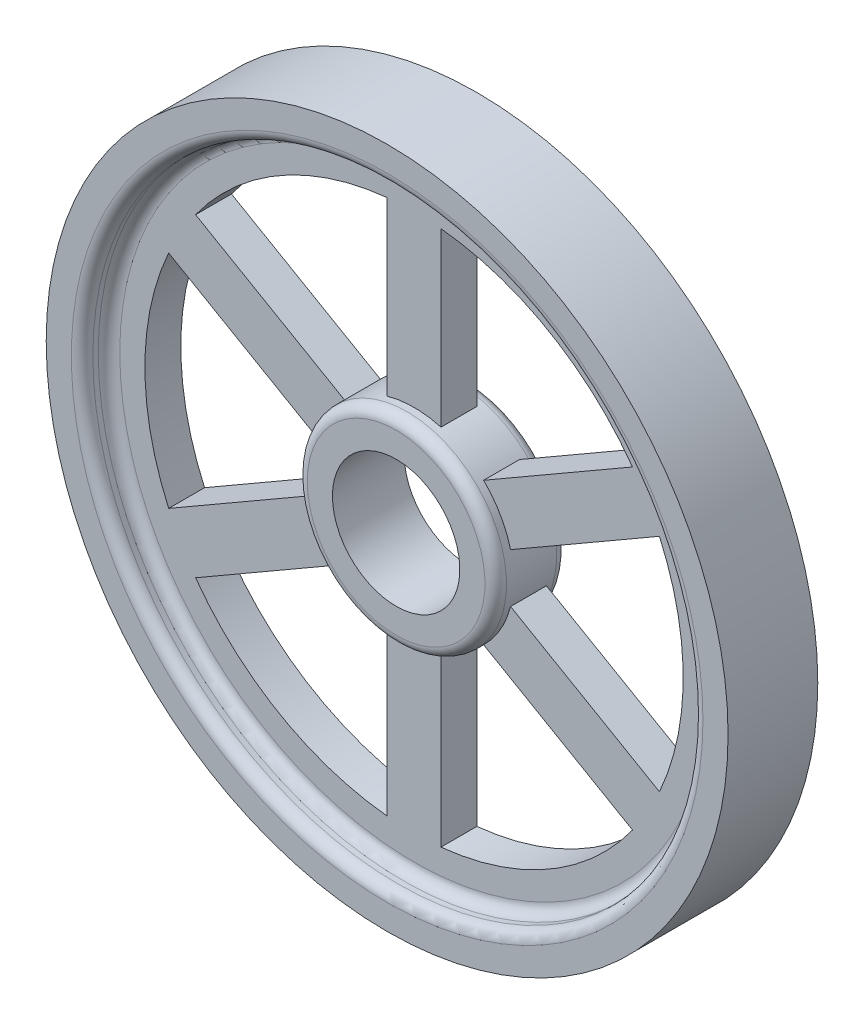
SolidWorks part; units mm, degrees
ref_plane "Front Plane" through (0, 0, 0) normal (0, 0, 1) x (1, 0, 0)
ref_plane "Top Plane" through (0, 0, 0) normal (0, 1, 0) x (1, 0, 0)
ref_plane "Right Plane" through (0, 0, 0) normal (1, 0, 0) x (0, 0, -1)
sketch "Sketch2" plane through (0, 0, 0) normal (0, 0, 1) x (1, 0, 0)
  line L0 (0, 35.4088) -> (0, -35.4088) construction
  circle A0 centre (0, 0) radius 95
  circle A2 centre (0, 0) radius 85
extrude "Boss-Extrude1" add sketch "Sketch2" along normal blind 25
ref_plane "Plane1" through (0, 0, 12.5) normal (0, 0, -1) x (-1, 0, 0)
sketch "Sketch5" plane through (0, 0, 12.5) normal (0, 0, -1) x (-1, 0, 0)
  circle A0 centre (0, 0) radius 17.75
  circle A1 centre (0, 0) radius 27.75
extrude "Boss-Extrude2" add sketch "Sketch5" along normal blind 10 and the other way blind 10 separate body
fillet "Fillet3" radius 3 2 edges at (-27.75, 0, 2.5) (-27.75, 0, 22.5)
sketch "Sketch7" plane through (0, 0, 12.5) normal (0, 0, -1) x (-1, 0, 0)
  circle A0 centre (0, 0) radius 75
  circle A1 centre (0, 0) radius 85
extrude "Boss-Extrude4" add sketch "Sketch7" along normal blind 5 and the other way blind 5
sketch "Sketch9" plane through (0, 0, 12.5) normal (0, 0, -1) x (-1, 0, 0)
  line L1 (7.5, 26.7173) -> (7.5, 74.6241)
  line L2 (-7.5, 26.7173) -> (-7.5, 74.6241)
  arc A0 (7.5, 26.7173) -> (-7.5, 26.7173) centre (0, 0) ccw
  arc A1 (7.5, 74.6241) -> (-7.5, 74.6241) centre (0, 0) ccw
extrude "Boss-Extrude5" add sketch "Sketch9" along normal blind 5 and the other way blind 5
fillet "Fillet4" radius 3 1 edges at (85, 0, 25)
fillet "Fillet8" radius 3 1 edges at (85, 0, 0)
fillet "Fillet9" radius 3 2 edges at (-85, 0, 17.5) (-85, 0, 7.5)
pattern_circular "CirPattern2" count 6 over 360 about axis through (0, 0, 0) along (0, 0, 1) of "Boss-Extrude5"
